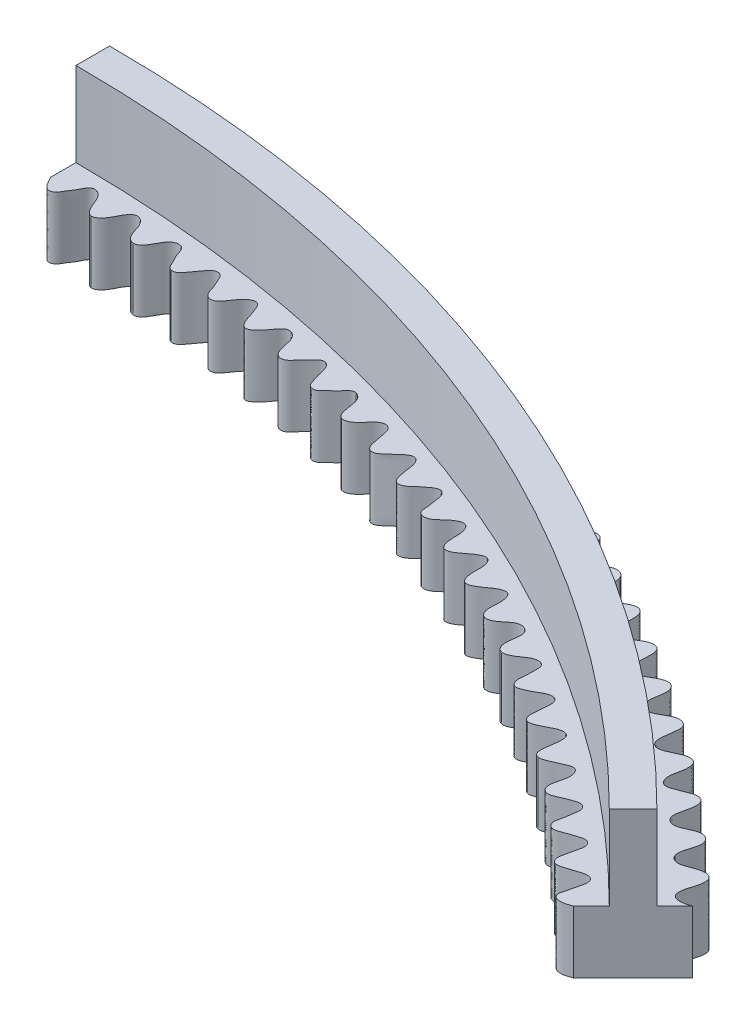
SolidWorks part; units mm, degrees
ref_plane "Front Plane" through (0, 0, 0) normal (0, 0, 1) x (1, 0, 0)
ref_plane "Top Plane" through (0, 0, 0) normal (0, 1, 0) x (1, 0, 0)
ref_plane "Right Plane" through (0, 0, 0) normal (1, 0, 0) x (0, 0, -1)
sketch "Sketch1" plane through (0, 0, 0) normal (0, 1, 0) x (1, 0, 0)
  spline S0 degree 4 number of poles 772 (76.8768, -22.0529) -> (-76.9201, -22.0639) construction
  spline S1 degree 4 number of poles 654 (80, 0) -> (-80, 0)
  spline S2 degree 4 number of poles 772 (-76.8768, 22.0529) -> (76.9201, 22.0639) construction
  spline S3 degree 4 number of poles 654 (-80, 0) -> (80, 0)
extrude "Boss-Extrude1" add sketch "Sketch1" along normal blind 3.7
sketch "Sketch2" plane through (0, 3.7, 0) normal (0, 1, 0) x (1, 0, 0)
  spline S0 degree 4 number of poles 790 (72.3028, -20.6224) -> (-71.9456, -20.5213) construction
  spline S1 degree 4 number of poles 670 (75, 0) -> (-75, 0)
  spline S2 degree 4 number of poles 790 (-72.3028, 20.6224) -> (71.9456, 20.5213) construction
  spline S3 degree 4 number of poles 670 (-75, 0) -> (75, 0)
extrude "Cut-Extrude1" cut sketch "Sketch2" against normal through all both and the other way through all
sketch "Sketch3" plane through (0, 3.7, 0) normal (0, 1, 0) x (1, 0, 0)
  circle A0 centre (0, 0) radius 76.5
  circle A1 centre (0, 0) radius 78.5
  dimension "D1" = 153
  dimension "D2" = 157
extrude "Boss-Extrude2" add sketch "Sketch3" along normal blind 5
sketch "Sketch4" plane through (0, 8.7, 0) normal (0, 1, 0) x (1, 0, 0)
  line L0 (0, 90) -> (0, 0)
  line L1 (0, 0) -> (63.6396, 63.6396)
  arc A0 (0, 90) -> (63.6396, 63.6396) centre (0, 0) ccw
  dimension "D2" = 90
  dimension "D1" = 45
extrude "Cut-Extrude2" cut sketch "Sketch4" against normal through all both and the other way through all
